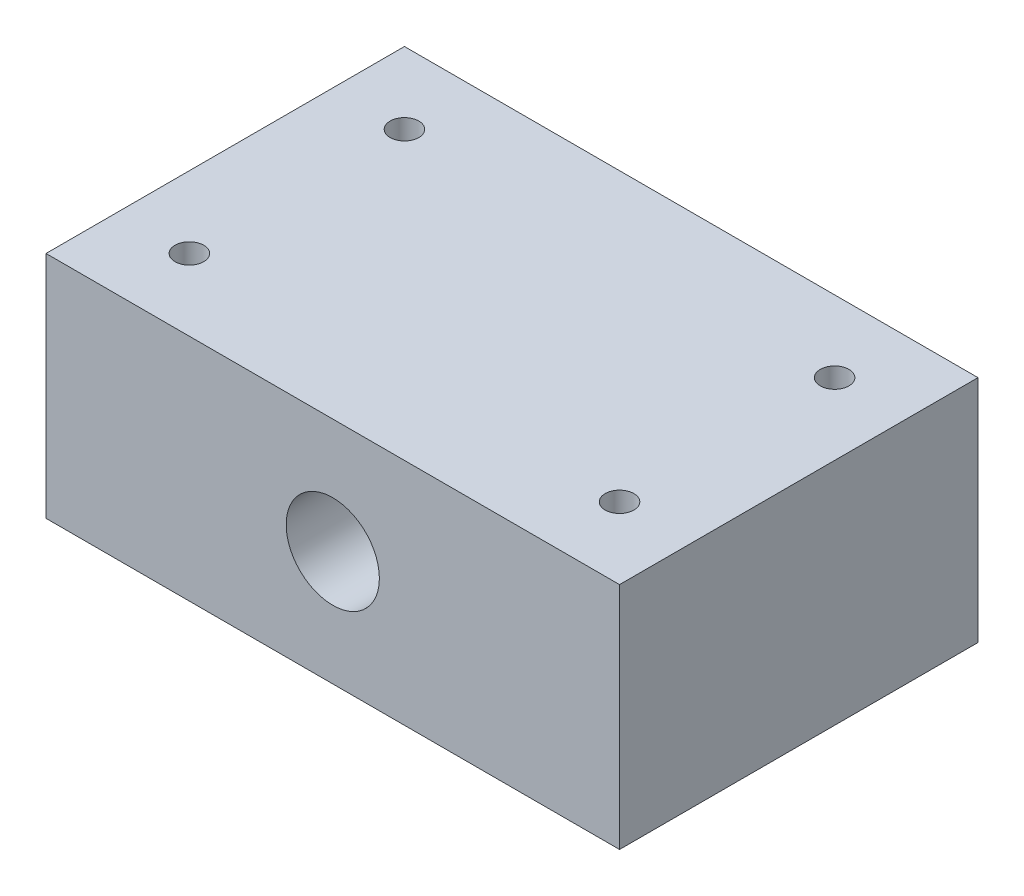
SolidWorks part; units mm, degrees
ref_plane "Front Plane" through (0, 0, 0) normal (0, 0, 1) x (1, 0, 0)
ref_plane "Top Plane" through (0, 0, 0) normal (0, 1, 0) x (1, 0, 0)
ref_plane "Right Plane" through (0, 0, 0) normal (1, 0, 0) x (0, 0, -1)
sketch "Sketch1" plane through (0, 0, 0) normal (0, 1, 0) x (1, 0, 0)
  line L0 (10, 40) -> (10, 10) construction
  line L1 (0, 0) -> (80, 0)
  line L2 (0, 0) -> (0, 50)
  line L3 (0, 50) -> (80, 50)
  line L4 (80, 0) -> (80, 50)
  line L5 (0, 0) -> (80, 50) construction
  line L6 (0, 50) -> (80, 0) construction
  line L7 (10, 10) -> (70, 10) construction
  line L8 (70, 10) -> (70, 40) construction
  circle A0 centre (10, 40) radius 2
  circle A1 centre (70, 40) radius 2
  circle A2 centre (70, 10) radius 2
  circle A3 centre (10, 10) radius 2
  point P4 (40, 25)
  point P14 (0, 0)
  point P15 (0, 0)
  point P16 (0, 0)
  point P17 (0, 0)
  dimension "D3" = 4
  dimension "D1" = 80
  dimension "D2" = 50
  dimension "D4" = 30
  dimension "D5" = 10
  dimension "D6" = 10
  dimension "D7" = 10
extrude "Boss-Extrude1" add sketch "Sketch1" along normal blind 32
sketch "Sketch2" plane through (0, 0, 0) normal (0, 0, 1) x (1, 0, 0)
  line L0 (0, 0) -> (80, 0) construction
  line L1 (0, 32) -> (80, 32) construction
  circle A0 centre (40, 16) radius 6.5
  point P4 (40, 0)
  point P5 (0, 0)
  dimension "D1" = 13
  dimension "D2" = 16
extrude "Cut-Extrude1" cut sketch "Sketch2" against normal through all
